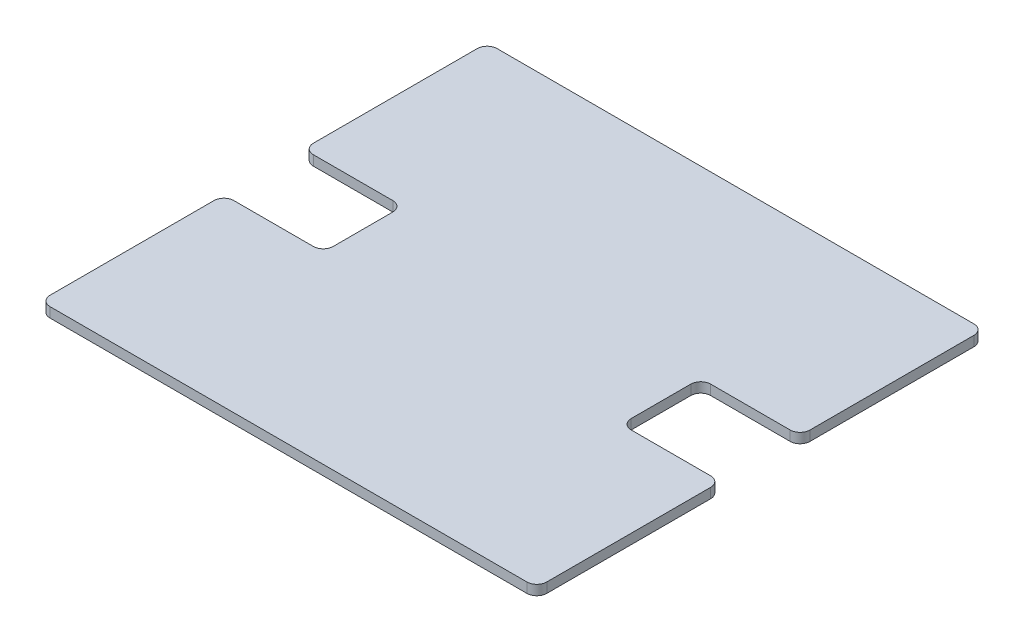
SolidWorks part; units mm, degrees
ref_plane "Front Plane" through (0, 0, 0) normal (0, 0, 1) x (1, 0, 0)
ref_plane "Top Plane" through (0, 0, 0) normal (0, 1, 0) x (1, 0, 0)
ref_plane "Right Plane" through (0, 0, 0) normal (1, 0, 0) x (0, 0, -1)
sketch "Sketch2" plane through (0, 0, 0) normal (0, 1, 0) x (1, 0, 0)
  line L0 (-50, 45) -> (50, 45)
  line L1 (50, 45) -> (50, 8)
  line L2 (50, 8) -> (30, 8)
  line L3 (30, 8) -> (30, -8)
  line L4 (-50, 45) -> (-50, 8)
  line L5 (-50, 8) -> (-30, 8)
  line L6 (-30, 8) -> (-30, -8)
  line L7 (-30, 0) -> (30, 0) construction
  line L8 (-50, -8) -> (-30, -8)
  line L9 (-50, -45) -> (-50, -8)
  line L10 (50, -8) -> (30, -8)
  line L11 (50, -45) -> (50, -8)
  line L12 (-50, -45) -> (50, -45)
  point P10 (0, 45)
  dimension "D1" = 100
  dimension "D2" = 45
  dimension "D3" = 8
  dimension "D4" = 20
extrude "Boss-Extrude1" add sketch "Sketch2" along normal blind 2
fillet "Fillet1" radius 2 12 edges at (50, 1, -45) (50, 1, -8) (30, 1, -8) (30, 1, 8) (50, 1, 8) (50, 1, 45) (-50, 1, 45) (-50, 1, -45) (-50, 1, 8) (-30, 1, 8) (-50, 1, -8) (-30, 1, -8)
